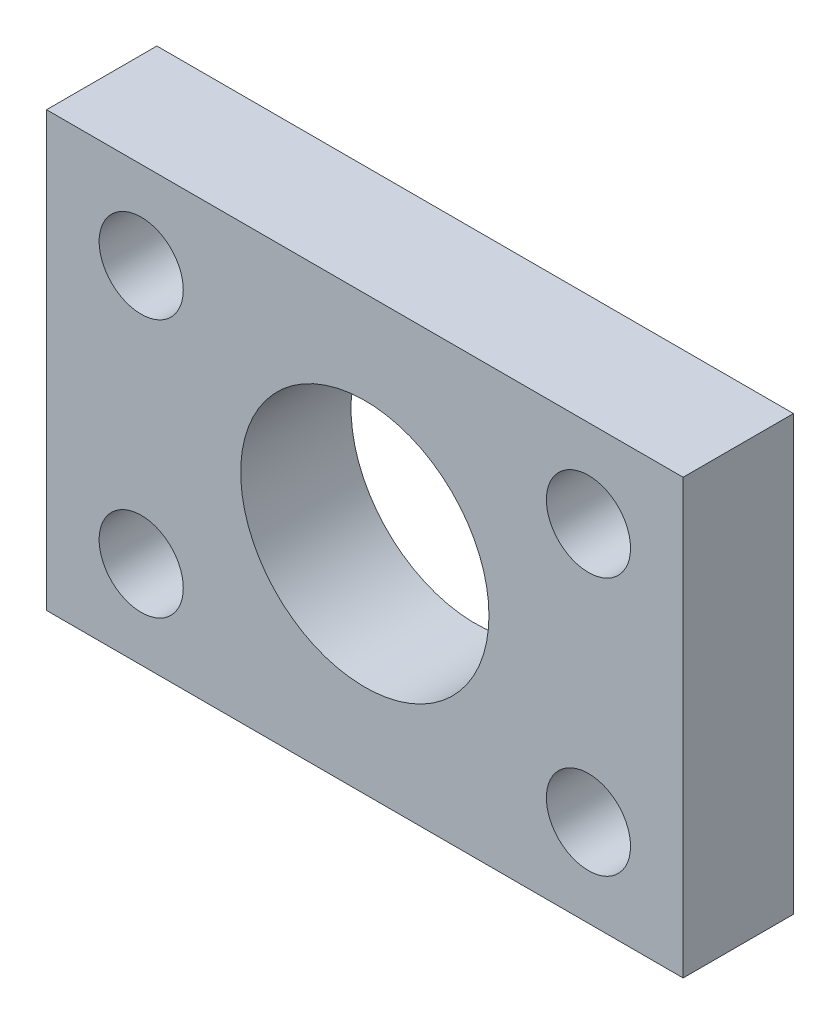
SolidWorks part; units mm, degrees
ref_plane "Front Plane" through (0, 0, 0) normal (0, 0, 1) x (1, 0, 0)
ref_plane "Top Plane" through (0, 0, 0) normal (0, 1, 0) x (1, 0, 0)
ref_plane "Right Plane" through (0, 0, 0) normal (1, 0, 0) x (0, 0, -1)
sketch "Sketch1" plane through (0, 0, 0) normal (0, 0, 1) x (1, 0, 0)
  line L0 (-5.5079, 3.18) -> (-8.106, 4.68) construction
  line L1 (7.3439, 0) -> (3.6719, 6.36)
  line L2 (3.6719, 6.36) -> (-3.6719, 6.36)
  line L3 (-3.6719, 6.36) -> (-7.3439, 0)
  line L4 (-7.3439, 0) -> (-3.6719, -6.36)
  line L5 (-3.6719, -6.36) -> (3.6719, -6.36)
  line L6 (3.6719, -6.36) -> (7.3439, 0)
  line L7 (-11.538, -7.86) -> (11.538, -7.86)
  line L8 (-11.538, -7.86) -> (-11.538, 7.86)
  line L9 (-11.538, 7.86) -> (11.538, 7.86)
  line L10 (11.538, -7.86) -> (11.538, 7.86)
  line L11 (-11.538, -7.86) -> (11.538, 7.86) construction
  line L12 (-11.538, 7.86) -> (11.538, -7.86) construction
  line L13 (-5.5079, -3.18) -> (-8.106, -4.68) construction
  line L14 (5.5079, -3.18) -> (8.106, -4.68) construction
  line L15 (5.5079, 3.18) -> (8.106, 4.68) construction
  line L16 (9.0759, 0) -> (4.538, 7.86) construction
  line L17 (4.538, 7.86) -> (-4.538, 7.86) construction
  line L18 (-4.538, 7.86) -> (-9.0759, 0) construction
  line L19 (-9.0759, 0) -> (-4.538, -7.86) construction
  line L20 (-4.538, -7.86) -> (4.538, -7.86) construction
  line L21 (4.538, -7.86) -> (9.0759, 0) construction
  circle A0 centre (0, 0) radius 6.36 construction
  circle A1 centre (-8.106, 4.68) radius 1.525
  circle A2 centre (8.106, 4.68) radius 1.525
  circle A3 centre (8.106, -4.68) radius 1.525
  circle A4 centre (-8.106, -4.68) radius 1.525
  circle A5 centre (0, 0) radius 4.5
  dimension "D4" = 3.05
  dimension "D7" = 9
  dimension "D1" = 12.72
  dimension "D2" = 1.5
  dimension "D3" = 1.5
  dimension "D5" = 3
  dimension "D6" = 7
extrude "Boss-Extrude2" add sketch "Sketch1" along normal blind 4 contours L7 L10 L9 L8 A4 A3 A2 A1 L6 L5 L4 L3 L2 L1 | L5 L6 L1 L2 L3 L4 A5
